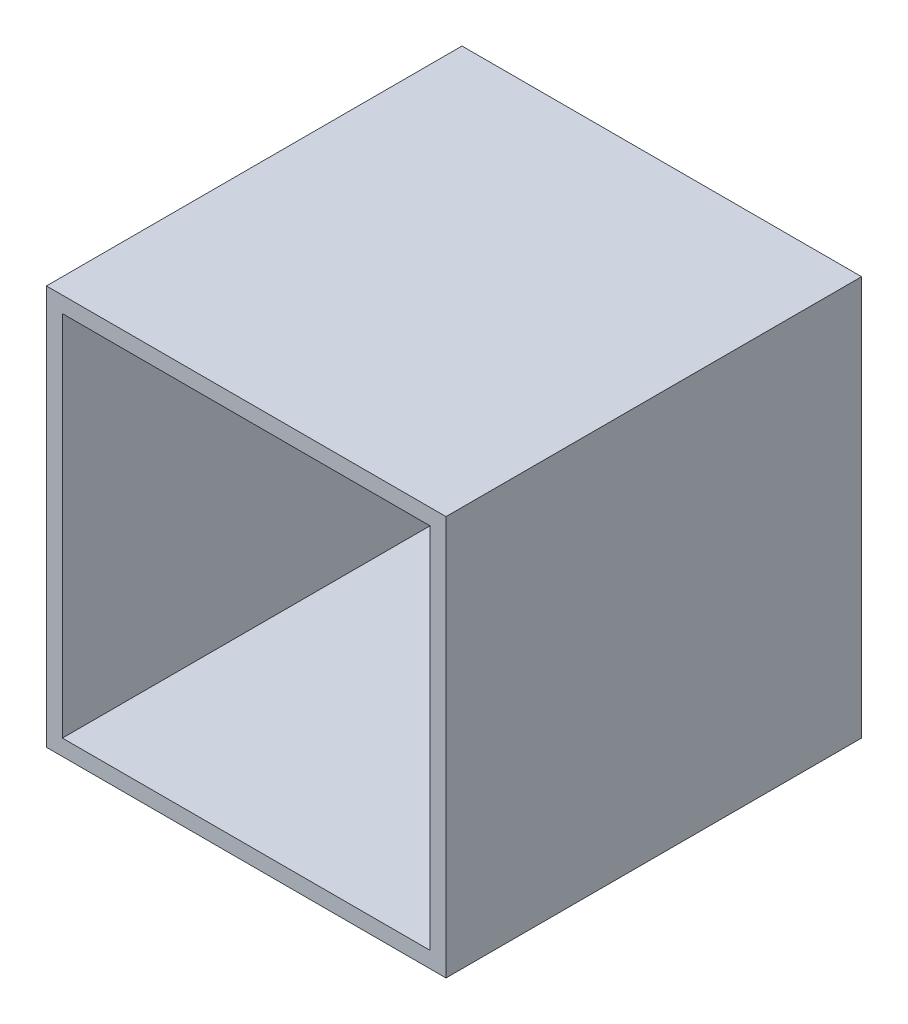
SolidWorks part; units mm, degrees
ref_plane "Alzado" through (0, 0, 0) normal (0, 0, 1) x (1, 0, 0)
ref_plane "Planta" through (0, 0, 0) normal (0, 1, 0) x (1, 0, 0)
ref_plane "Vista lateral" through (0, 0, 0) normal (1, 0, 0) x (0, 0, -1)
sketch "Croquis1" plane through (0, 0, 0) normal (0, 0, 1) x (1, 0, 0)
  line L1 (-77.8929, 38.1849) -> (-27.8929, 38.1849)
  line L2 (-77.8929, 38.1849) -> (-77.8929, -11.8151)
  line L3 (-77.8929, -11.8151) -> (-27.8929, -11.8151)
  line L4 (-27.8929, 38.1849) -> (-27.8929, -11.8151)
  dimension "D1" = 50
  dimension "D2" = 50
extrude "Saliente-Extruir1" add sketch "Croquis1" along normal blind 52
sketch "Croquis2" plane through (0, 0, 52) normal (0, 0, 1) x (1, 0, 0)
  line L0 (-27.8929, 38.1849) -> (-77.8929, 38.1849) construction
  line L1 (-75.8929, -9.8151) -> (-29.8929, -9.8151)
  line L2 (-75.8929, -9.8151) -> (-75.8929, 36.1849)
  line L3 (-75.8929, 36.1849) -> (-29.8929, 36.1849)
  line L4 (-29.8929, -9.8151) -> (-29.8929, 36.1849)
  line L5 (-75.8929, -9.8151) -> (-29.8929, 36.1849) construction
  line L6 (-75.8929, 36.1849) -> (-29.8929, -9.8151) construction
  line L7 (-77.8929, 38.1849) -> (-77.8929, -11.8151) construction
  point P0 (-52.8929, 13.1849)
  dimension "D1" = 46
  dimension "D2" = 46
  dimension "D3" = 2
  dimension "D4" = 2
extrude "Cortar-Extruir1" cut sketch "Croquis2" against normal blind 50
